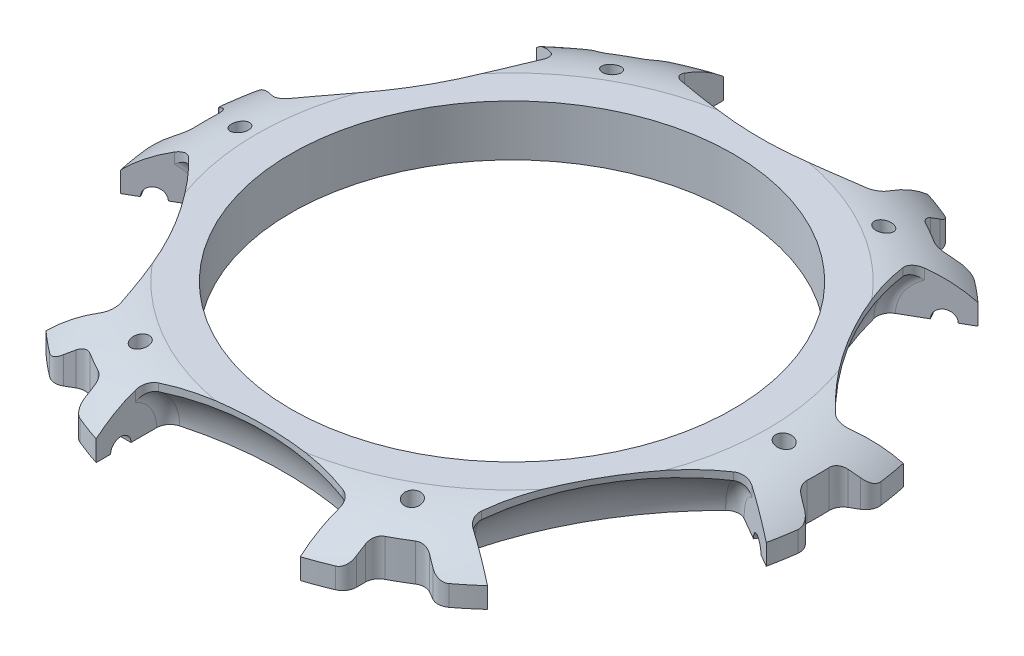
SolidWorks part; units mm, degrees
ref_plane "Front Plane" through (0, 0, 0) normal (0, 0, 1) x (1, 0, 0)
ref_plane "Top Plane" through (0, 0, 0) normal (0, 1, 0) x (1, 0, 0)
ref_plane "Right Plane" through (0, 0, 0) normal (1, 0, 0) x (0, 0, -1)
sketch "Sketch1" plane through (0, 0, 0) normal (0, 1, 0) x (1, 0, 0)
  line L10 (0, 0) -> (0, -50) construction
  line L11 (15, -42.5) -> (-15, -42.5) construction
  line L12 (15, -37.303) -> (15, -47.697)
  line L13 (-15, -37.303) -> (-15, -47.697)
  line L14 (-24.8054, -31.6419) -> (-33.8068, -36.8389)
  line L15 (-39.8054, -5.6611) -> (-48.8068, -10.8581)
  line L16 (-29.3061, -34.2404) -> (-44.3061, -8.2596) construction
  line L17 (-39.8054, 5.6611) -> (-48.8068, 10.8581)
  line L18 (-24.8054, 31.6419) -> (-33.8068, 36.8389)
  line L19 (-44.3061, 8.2596) -> (-29.3061, 34.2404) construction
  line L20 (-15, 37.303) -> (-15, 47.697)
  line L21 (15, 37.303) -> (15, 47.697)
  line L22 (-15, 42.5) -> (15, 42.5) construction
  line L23 (24.8054, 31.6419) -> (33.8068, 36.8389)
  line L24 (39.8054, 5.6611) -> (48.8068, 10.8581)
  line L25 (29.3061, 34.2404) -> (44.3061, 8.2596) construction
  line L26 (39.8054, -5.6611) -> (48.8068, -10.8581)
  line L27 (24.8054, -31.6419) -> (33.8068, -36.8389)
  line L28 (44.3061, -8.2596) -> (29.3061, -34.2404) construction
  line L103 (-16.5, -36.2148) -> (-16.5, -47.697)
  line L104 (16.5, -36.2148) -> (16.5, -47.697)
  circle A3 centre (0, 0) radius 50
  circle A4 centre (0, 0) radius 42.5 construction
  arc A8 (-15, -37.303) -> (15, -37.303) centre (0, -85) cw
  arc A9 (-39.8054, -5.6611) -> (-24.8054, -31.6419) centre (-73.6122, -42.5) cw
  arc A10 (-24.8054, 31.6419) -> (-39.8054, 5.6611) centre (-73.6122, 42.5) cw
  arc A11 (15, 37.303) -> (-15, 37.303) centre (0, 85) cw
  arc A12 (39.8054, 5.6611) -> (24.8054, 31.6419) centre (73.6122, 42.5) cw
  arc A13 (24.8054, -31.6419) -> (39.8054, -5.6611) centre (73.6122, -42.5) cw
  circle A38 centre (0, 0) radius 33.5
  circle A39 centre (0, 0) radius 28
  arc A40 (-16.5, -36.2148) -> (16.5, -36.2148) centre (0, -85) cw
  circle A41 centre (0, 0) radius 31
  point P18 (0, -42.5)
  point P28 (-36.8061, -21.25)
  point P36 (-36.8061, 21.25)
  point P44 (0, 42.5)
  point P52 (36.8061, 21.25)
  point P60 (36.8061, -21.25)
  point P65 (0, 0)
  dimension "D1" = 30
  dimension "D2" = 100
  dimension "D3" = 85
  dimension "D4" = 6
  dimension "D5" = 1.5
  dimension "D6" = 2.5
  dimension "D7" = 3
sketch "Sketch2" plane through (0, 0, 0) normal (0, 1, 0) x (1, 0, 0)
  circle A0 centre (0, 0) radius 50 construction
  circle A1 centre (0, 0) radius 50
extrude "Boss-Extrude1" add sketch "Sketch2" along normal blind 7.5
sketch "Sketch3" plane through (0, 0, 0) normal (0, 1, 0) x (1, 0, 0)
  line L5 (-20.18, -42.5) -> (20.5663, -42.5) construction
  line L6 (-15, -42.5) -> (15, -42.5)
  line L7 (-15, -42.5) -> (-15, -35.7329)
  line L8 (15, -42.5) -> (15, -35.7329)
  arc A0 (16.5, -36.2148) -> (-16.5, -36.2148) centre (0, -85) ccw construction
  arc A1 (15, -35.7329) -> (-15, -35.7329) centre (0, -85) ccw
revolve "Cut-Revolve1" cut sketch "Sketch3" angle 360 about L5
sketch "Sketch4" plane through (0, 0, 0) normal (0, 1, 0) x (1, 0, 0)
  line L5 (15, -38.8779) -> (15, -47.697)
  line L6 (-15, -37.303) -> (-15, -47.697) construction
  line L7 (-15, -38.8779) -> (-15, -47.697)
  arc A0 (16.5, -36.2148) -> (-16.5, -36.2148) centre (0, -85) ccw construction
  arc A1 (16.5, -36.2148) -> (-16.5, -36.2148) centre (0, -85) ccw construction
  arc A2 (15, -38.8779) -> (-15, -38.8779) centre (0, -85) ccw
  circle A3 centre (0, 0) radius 50 construction
  arc A4 (-15, -47.697) -> (15, -47.697) centre (0, 0) ccw
  dimension "D1" = 3
extrude "Cut-Extrude2" cut sketch "Sketch4" along normal up to next (7.5 mm away)
sketch "Sketch5" plane through (0, 0, 0) normal (1, 0, 0) x (0, 0, -1)
  circle A0 centre (-42.5, 0) radius 1.5
  point P0 (-42.5, 0)
  dimension "D1" = 3
extrude "Cut-Extrude3" cut sketch "Sketch5" against normal blind 18 and the other way blind 18
pattern_circular "CirPattern1" count 6 over 360 about axis through (0, 0, 0) along (0, 1, 0) of "Cut-Revolve1", "Cut-Extrude2", "Cut-Extrude3"
sketch "Sketch6" plane through (0, 0, 0) normal (0, -1, 0) x (1, 0, 0)
  line L0 (-29.1051, 37.5885) -> (-26.507, 36.0885) construction
  line L1 (-18, 44) -> (-18, 41) construction
  line L2 (-29.1051, 37.5885) -> (-26.507, 36.0885) construction
  line L3 (-18, 44) -> (-18, 41) construction
  line L4 (-20, 44) -> (-20, 41) construction
  line L5 (-28.1051, 39.3205) -> (-25.507, 37.8205) construction
  line L6 (-28.2647, 39.4126) -> (-24.9106, 37.4762)
  line L7 (-20, 40.3113) -> (-20, 44.1843)
  line L8 (20, 44.1843) -> (20, 40.3113)
  line L9 (24.9106, 37.4762) -> (28.2647, 39.4126)
  line L10 (48.2647, 4.7716) -> (44.9106, 2.8351)
  line L11 (44.9106, -2.8351) -> (48.2647, -4.7716)
  line L12 (28.2647, -39.4126) -> (24.9106, -37.4762)
  line L13 (20, -40.3113) -> (20, -44.1843)
  line L14 (-20, -44.1843) -> (-20, -40.3113)
  line L15 (-24.9106, -37.4762) -> (-28.2647, -39.4126)
  line L16 (-48.2647, -4.7716) -> (-44.9106, -2.8351)
  line L17 (-44.9106, 2.8351) -> (-48.2647, 4.7716)
  circle A1 centre (0, 0) radius 50 construction
  arc A4 (-20, 40.3113) -> (-24.9106, 37.4762) centre (0, 0) ccw
  arc A5 (-28.2647, 39.4126) -> (-48.2647, 4.7716) centre (0, 0) ccw
  arc A6 (24.9106, 37.4762) -> (20, 40.3113) centre (0, 0) ccw
  circle A7 centre (0, 0) radius 50
  arc A10 (44.9106, -2.8351) -> (44.9106, 2.8351) centre (0, 0) ccw
  arc A12 (20, -40.3113) -> (24.9106, -37.4762) centre (0, 0) ccw
  arc A14 (-24.9106, -37.4762) -> (-20, -40.3113) centre (0, 0) ccw
  arc A16 (-44.9106, 2.8351) -> (-44.9106, -2.8351) centre (0, 0) ccw
  arc A18 (20, 44.1843) -> (-20, 44.1843) centre (0, 0) ccw
  arc A19 (48.2647, 4.7716) -> (28.2647, 39.4126) centre (0, 0) ccw
  arc A20 (28.2647, -39.4126) -> (48.2647, -4.7716) centre (0, 0) ccw
  arc A21 (-20, -44.1843) -> (20, -44.1843) centre (0, 0) ccw
  arc A22 (-48.2647, -4.7716) -> (-28.2647, -39.4126) centre (0, 0) ccw
  point P1 (48.5, 0)
  point P15 (43.0337, 13.1567)
  point P48 (0, 0)
  dimension "D5" = 6
  dimension "D3" = 2
  dimension "D4" = 2
extrude "Cut-Extrude4" cut sketch "Sketch6" against normal up to next
sketch "Sketch8" plane through (0, 0, 0) normal (0, -1, 0) x (1, 0, 0)
  circle A2 centre (0, 0) radius 32.5
  circle A3 centre (0, 0) radius 32.5
  dimension "D1" = 1
extrude "Cut-Extrude5" cut sketch "Sketch8" against normal up to next
sketch "Sketch9" plane through (0, 0, 0) normal (0, -1, 0) x (1, 0, 0)
  line L0 (0, 0) -> (32.5, 0) construction
  line L1 (32.5, 0) -> (40, 0) construction
  circle A0 centre (0, 0) radius 32.5 construction
  circle A1 centre (40, 0) radius 1.25
  dimension "D2" = 2.5
  dimension "D1" = 40
extrude "Cut-Extrude6" cut sketch "Sketch9" against normal up to next (7.5 mm away)
sketch "Sketch10" plane through (0, 7.5, 0) normal (0, 1, 0) x (1, 0, 0)
  line L1 (40, 3.4641) -> (37, 1.7321)
  line L2 (37, 1.7321) -> (37, -1.7321)
  line L3 (37, -1.7321) -> (40, -3.4641)
  line L4 (40, -3.4641) -> (43, -1.7321)
  line L5 (43, -1.7321) -> (43, 1.7321)
  line L6 (43, 1.7321) -> (40, 3.4641)
  circle A0 centre (40, 0) radius 3 construction
  circle A1 centre (40, 0) radius 3 construction
pattern_circular "CirPattern2" count 6 over 360 about axis through (0, 0, 0) along (0, 1, 0) of "Cut-Extrude6"
sketch "Sketch7" plane through (0, 0, 0) normal (0, 0, 1) x (1, 0, 0)
  line L0 (-50, 0) -> (-50, 1.5) construction
  line L1 (50, 0) -> (-50, 0) construction
  line L2 (-26.1692, 7.5) -> (-41.1692, 7.5) construction
  line L3 (-37.542, 7.5) -> (-50, 7.5)
  line L4 (-50, 7.5) -> (-50, 1.5)
  line L5 (0, 0) -> (0, 7.5) construction
  line L6 (15, 7.5) -> (-15, 7.5) construction
  spline S0 degree 2 poles (-50, 1.5) (-45.2094, 6.974) (-37.542, 7.5) knots 0 0 0 1 1 1
revolve "Cut-Revolve2" cut sketch "Sketch7" angle 360 about L5
fillet "Fillet1" radius 2 12 edges at (-44.9106, 2.7403, -2.8351) (-44.9106, 2.7403, 2.8351) (-20, 2.7403, -40.3113) (-24.9106, 2.7403, -37.4762) (24.9106, 2.7403, -37.4762) (20, 2.7403, -40.3113) (44.9106, 2.7403, 2.8351) (44.9106, 2.7403, -2.8351) (24.9106, 2.7403, 37.4762) (20, 2.7403, 40.3113) (-20, 2.7403, 40.3113) (-24.9106, 2.7403, 37.4762)
fillet "Fillet2" radius 2 24 edges at (24.1714, 3.2621, -31.2759) (26.1692, 6.2583, -32.4293) (39.1714, 3.2621, -5.2951) (41.1692, 6.2583, -6.4486) (39.1714, 3.2621, 5.2951) (41.1692, 6.2583, 6.4486) (24.1714, 3.2621, 31.2759) (26.1692, 6.2583, 32.4293) (15, 6.2583, 38.8779) (15, 3.2621, 36.571) (-15, 3.2621, 36.571) (-15, 6.2583, 38.8779) (-26.1692, 6.2583, 32.4293) (-24.1714, 3.2621, 31.2759) (-41.1692, 6.2583, 6.4486) (-39.1714, 3.2621, 5.2951) (-41.1692, 6.2583, -6.4486) (-39.1714, 3.2621, -5.2951) (-26.1692, 6.2583, -32.4293) (-24.1714, 3.2621, -31.2759) (-15, 6.2583, -38.8779) (-15, 3.2621, -36.571) (15, 3.2621, -36.571) (15, 6.2583, -38.8779)
fillet "Fillet3" radius 2 12 edges at (-48.2647, 1.5146, 4.7716) (-48.2647, 1.5146, -4.7716) (-28.2647, 1.5146, -39.4126) (-20, 1.5146, -44.1843) (20, 1.5146, -44.1843) (28.2647, 1.5146, -39.4126) (48.2647, 1.5146, -4.7716) (48.2647, 1.5146, 4.7716) (20, 1.5146, 44.1843) (28.2647, 1.5146, 39.4126) (-28.2647, 1.5146, 39.4126) (-20, 1.5146, 44.1843)
